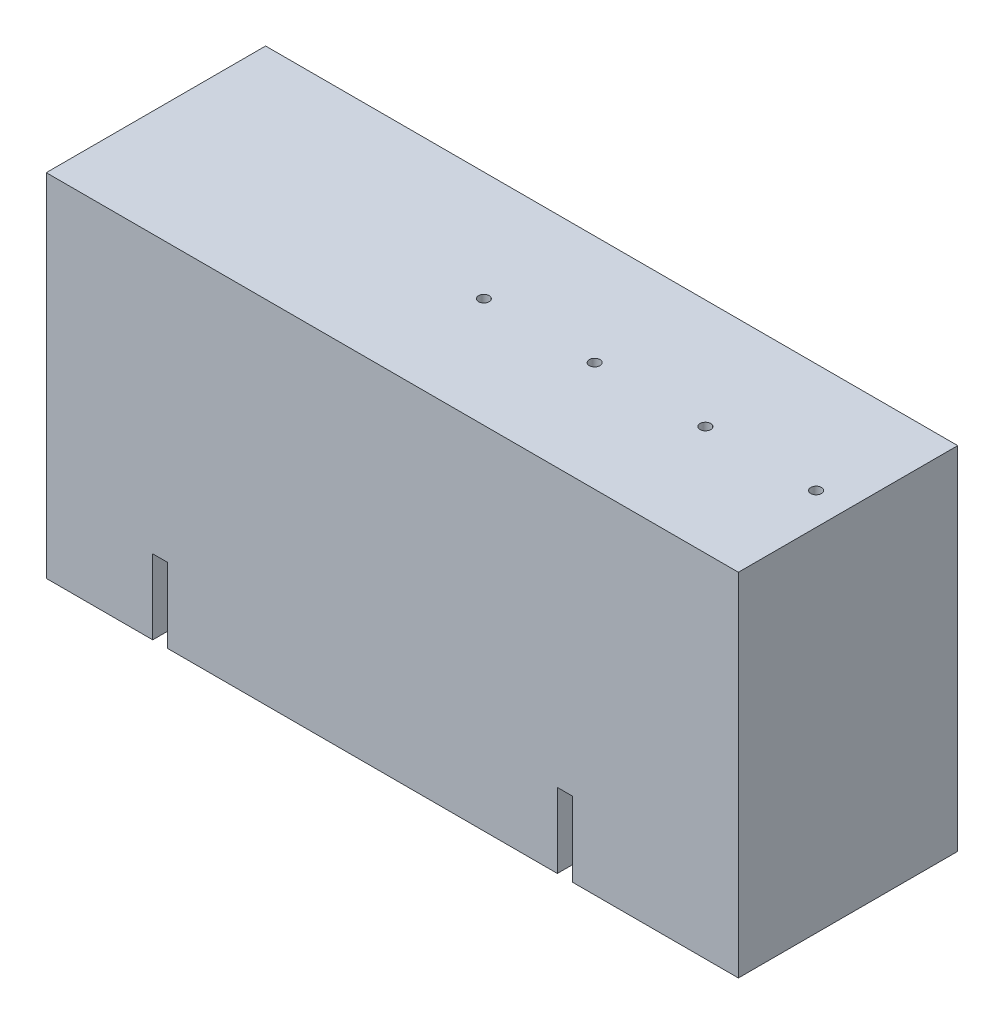
SolidWorks part; units mm, degrees
ref_plane "Front Plane" through (0, 0, 0) normal (0, 0, 1) x (1, 0, 0)
ref_plane "Top Plane" through (0, 0, 0) normal (0, 1, 0) x (1, 0, 0)
ref_plane "Right Plane" through (0, 0, 0) normal (1, 0, 0) x (0, 0, -1)
sketch "Sketch1" plane through (0, 0, 0) normal (0, 1, 0) x (1, 0, 0)
  line L1 (0, 0) -> (325, 0)
  line L2 (0, 0) -> (0, 103)
  line L3 (0, 103) -> (325, 103)
  line L4 (325, 0) -> (325, 103)
  dimension "D1" = 103
  dimension "D2" = 325
extrude "Boss-Extrude1" add sketch "Sketch1" along normal blind 165
sketch "Sketch2" plane through (0, 165, 0) normal (0, 1, 0) x (1, 0, 0)
  line L0 (325, 0) -> (325, 103) construction
  point P0 (310, 51.5)
  point P1 (258, 51.5)
  point P2 (206, 51.5)
  point P3 (154, 51.5)
  point P6 (325, 51.5)
  dimension "D1" = 15
  dimension "D2" = 52
  dimension "D3" = 52
  dimension "D4" = 52
hole_wizard "M6 Tapped Hole1" positions "Sketch3" profile "Sketch4" tap size "M6" standard "ISO"
sketch "Sketch3" plane through (0, 165, 0) normal (0, 1, 0) x (1, 0, 0)
  point P0 (310, 51.5)
  point P3 (258, 51.5)
  point P6 (206, 51.5)
  point P9 (154, 51.5)
sketch "Sketch4" plane through (310, 165, -51.5) normal (1, 0, 0) x (0, 0, 1)
  line L0 (0, 0) -> (0, 16.5022)
  line L1 (0, 16.5022) -> (2.5, 15)
  line L2 (2.5, 15) -> (2.5, 0)
  line L5 (2.5, 0) -> (0, 0)
  line L10 (0, 16.5022) -> (-2.5, 15) construction
  line L11 (0, -6.35) -> (0, 107.95) construction
  dimension "Tap Drill Dia." = 5
  dimension "Tap Drill Depth" = 15
  dimension "Drill Angle" = 118
cosmetic thread "Hole Thread1" parameters "D1"=12, "D2"=6
cosmetic thread "Hole Thread2" parameters "D1"=12, "D2"=6
cosmetic thread "Hole Thread3" parameters "D1"=12, "D2"=6
cosmetic thread "Hole Thread4" parameters "D1"=12, "D2"=6
sketch "Sketch5" plane through (0, 0, 0) normal (0, -1, 0) x (1, 0, 0)
  line L0 (50, 0) -> (50, -11.5)
  line L1 (0, 0) -> (325, 0) construction
  line L2 (50, 0) -> (57, 0)
  line L3 (57, 0) -> (57, -11.5)
  line L4 (0, -103) -> (0, 0) construction
  line L5 (0, -51.5) -> (325, -51.5) construction
  line L6 (325, 0) -> (325, -103) construction
  line L9 (247, 0) -> (247, -11.5)
  line L10 (247, 0) -> (240, 0)
  line L11 (240, 0) -> (240, -11.5)
  line L12 (247, -103) -> (240, -103)
  line L13 (240, -103) -> (240, -91.5)
  line L14 (247, -103) -> (247, -91.5)
  line L15 (50, -103) -> (50, -91.5)
  line L16 (50, -103) -> (57, -103)
  line L17 (57, -103) -> (57, -91.5)
  arc A0 (50, -11.5) -> (57, -11.5) centre (53.5, -11.5) ccw
  arc A1 (247, -11.5) -> (240, -11.5) centre (243.5, -11.5) cw
  arc A2 (247, -91.5) -> (240, -91.5) centre (243.5, -91.5) ccw
  arc A3 (50, -91.5) -> (57, -91.5) centre (53.5, -91.5) cw
  dimension "D1" = 7
  dimension "D2" = 11.5
  dimension "D3" = 50
  dimension "D4" = 190
extrude "Cut-Extrude1" cut sketch "Sketch5" against normal blind 35
